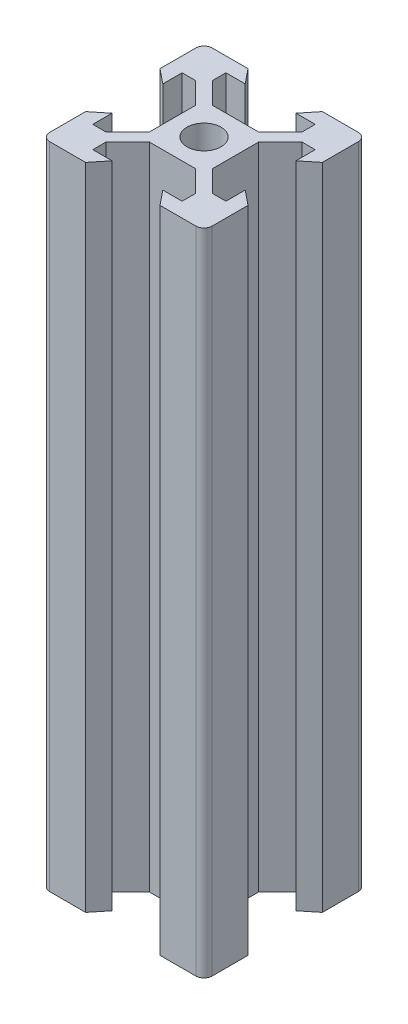
SolidWorks part; units mm, degrees
ref_plane "Front Plane" through (0, 0, 0) normal (0, 0, 1) x (1, 0, 0)
ref_plane "Top Plane" through (0, 0, 0) normal (0, 1, 0) x (1, 0, 0)
ref_plane "Right Plane" through (0, 0, 0) normal (1, 0, 0) x (0, 0, -1)
sketch "Sketch1" plane through (0, 0, 0) normal (0, 1, 0) x (1, 0, 0)
  line L0 (-3.125, 8.2) -> (-4.58, 10)
  line L1 (-9, 10) -> (9, 10)
  line L2 (-10, 9) -> (-10, -9)
  line L3 (-9, -10) -> (9, -10)
  line L4 (10, 9) -> (10, -9)
  line L5 (-10, 10) -> (10, -10) construction
  line L6 (-10, -10) -> (10, 10) construction
  line L7 (-10, 0) -> (0, 0) construction
  line L8 (0, 10) -> (0, 0) construction
  line L9 (-8.2, 3.125) -> (-10, 4.58)
  line L10 (-8.2, 3.125) -> (-8.2, 5.5)
  line L11 (-3.125, 8.2) -> (-5.5, 8.2)
  line L12 (-5.5, 8.2) -> (-5.5, 6.56)
  line L13 (-2.84, 3.9) -> (2.84, 3.9)
  line L14 (-5.5, 6.56) -> (-2.84, 3.9)
  line L15 (-8.2, 5.5) -> (-6.56, 5.5)
  line L16 (-6.56, 5.5) -> (-3.9, 2.84)
  line L17 (-3.9, 2.84) -> (-3.9, -2.84)
  line L18 (3.9, 2.84) -> (3.9, -2.84)
  line L19 (6.56, 5.5) -> (3.9, 2.84)
  line L20 (8.2, 5.5) -> (6.56, 5.5)
  line L21 (8.2, 3.125) -> (8.2, 5.5)
  line L22 (8.2, 3.125) -> (10, 4.58)
  line L23 (3.125, 8.2) -> (4.58, 10)
  line L24 (3.125, 8.2) -> (5.5, 8.2)
  line L25 (5.5, 8.2) -> (5.5, 6.56)
  line L26 (5.5, 6.56) -> (2.84, 3.9)
  line L27 (-8.2, -3.125) -> (-10, -4.58)
  line L28 (-8.2, -3.125) -> (-8.2, -5.5)
  line L29 (-8.2, -5.5) -> (-6.56, -5.5)
  line L30 (-6.56, -5.5) -> (-3.9, -2.84)
  line L31 (8.2, -3.125) -> (10, -4.58)
  line L32 (8.2, -3.125) -> (8.2, -5.5)
  line L33 (8.2, -5.5) -> (6.56, -5.5)
  line L34 (6.56, -5.5) -> (3.9, -2.84)
  line L35 (5.5, -6.56) -> (2.84, -3.9)
  line L36 (5.5, -8.2) -> (5.5, -6.56)
  line L37 (3.125, -8.2) -> (5.5, -8.2)
  line L38 (3.125, -8.2) -> (4.58, -10)
  line L39 (-5.5, -6.56) -> (-2.84, -3.9)
  line L40 (-2.84, -3.9) -> (2.84, -3.9)
  line L41 (-5.5, -8.2) -> (-5.5, -6.56)
  line L42 (-3.125, -8.2) -> (-5.5, -8.2)
  line L43 (-3.125, -8.2) -> (-4.58, -10)
  circle A0 centre (0, 0) radius 2.1
  arc A1 (-10, -9) -> (-9, -10) centre (-9, -9) ccw
  arc A2 (9, -10) -> (10, -9) centre (9, -9) ccw
  arc A3 (9, 10) -> (10, 9) centre (9, 9) cw
  arc A4 (-9, 10) -> (-10, 9) centre (-9, 9) ccw
  point P0 (0, 0)
  point P35 (0, 3.9)
  point P40 (-3.9, 0)
  point P41 (3.9, 0)
  dimension "D3" = 4.2
  dimension "D2" = 1
  dimension "D1" = 20
  dimension "D4" = 6.1
  dimension "D5" = 6.25
  dimension "D6" = 11
  dimension "D7" = 5.68
  dimension "D8" = 9.16
  dimension "D9" = 1.8
extrude "Boss-Extrude1" add sketch "Sketch1" along normal blind 80 contours L43 L42 L41 L39 L40 L35 L36 L37 L38 L3 L4 L31 L32 L33 L34 L18 L19 L20 L21 L22 L1 L23 L24 L25 L26 L13 L14 L12 L11 L0 L2 L9 L10 L15 L16 L17 L30 L29 L28 L27 A0
